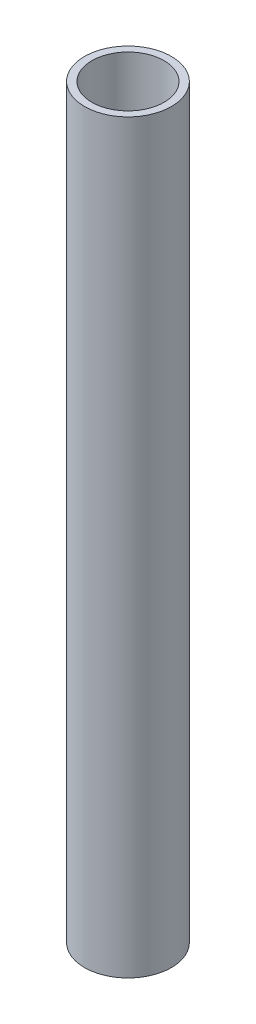
SolidWorks part; units mm, degrees
ref_plane "Front Plane" through (0, 0, 0) normal (0, 0, 1) x (1, 0, 0)
ref_plane "Top Plane" through (0, 0, 0) normal (0, 1, 0) x (1, 0, 0)
ref_plane "Right Plane" through (0, 0, 0) normal (1, 0, 0) x (0, 0, -1)
sketch "Sketch1" plane through (0, 0, 0) normal (0, 1, 0) x (1, 0, 0)
  circle A0 centre (0, 0) radius 21.082
  circle A1 centre (0, 0) radius 17.526
  dimension "D1" = 42.164
  dimension "D2" = 35.052
extrude "Boss-Extrude1" add sketch "Sketch1" along normal blind 361.95
